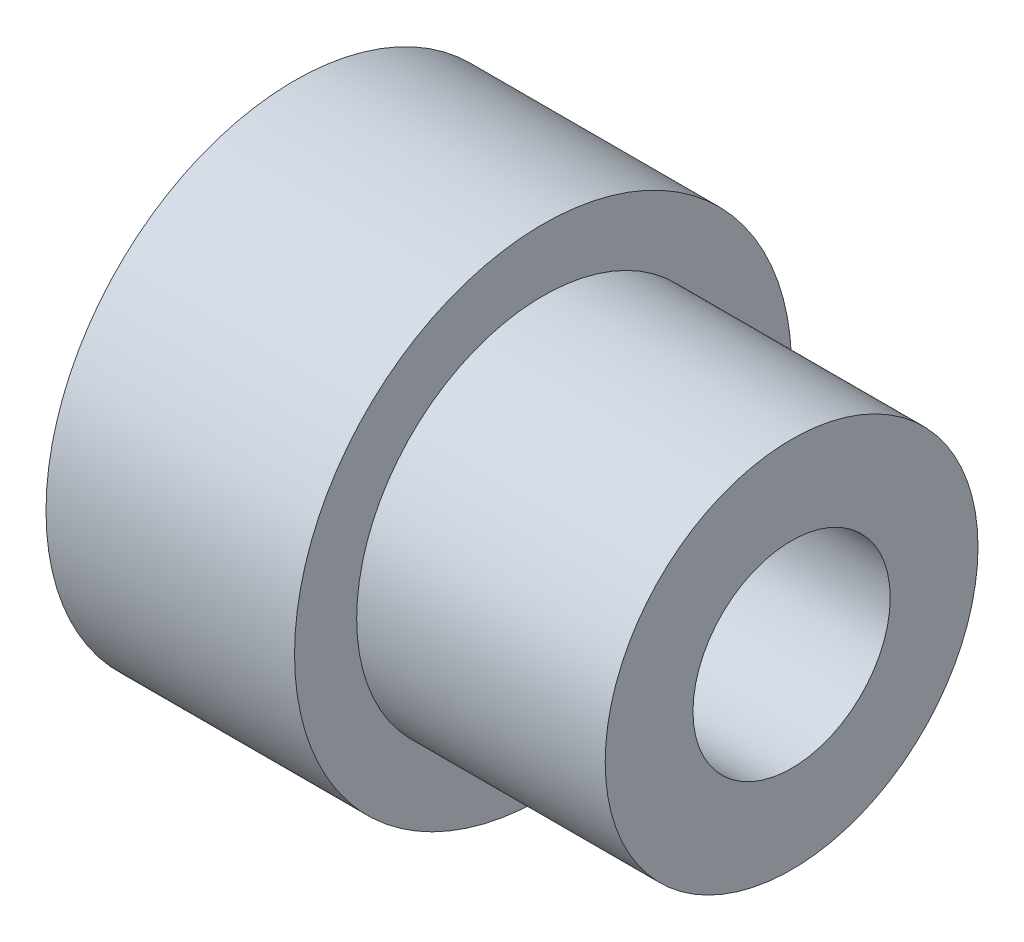
SolidWorks part; units mm, degrees
ref_plane "Front Plane" through (0, 0, 0) normal (0, 0, 1) x (1, 0, 0)
ref_plane "Top Plane" through (0, 0, 0) normal (0, 1, 0) x (1, 0, 0)
ref_plane "Right Plane" through (0, 0, 0) normal (1, 0, 0) x (0, 0, -1)
sketch "Sketch2" plane through (0, 0, 0) normal (1, 0, 0) x (0, 0, -1)
  circle A0 centre (0, 0) radius 6
  dimension "D1" = 12
extrude "Boss-Extrude1" add sketch "Sketch2" along normal blind 8
sketch "Sketch3" plane through (0, 0, 0) normal (-1, 0, 0) x (0, 0, 1)
  circle A0 centre (0, 0) radius 8
  dimension "D1" = 16
extrude "Boss-Extrude2" add sketch "Sketch3" along normal blind 8
sketch "Sketch4" plane through (8, 0, 0) normal (1, 0, 0) x (0, 0, -1)
  circle A0 centre (0, 0) radius 3.175
  dimension "D1" = 6.35
extrude "Cut-Extrude1" cut sketch "Sketch4" against normal through all
equation "\"wheelPitchD\"= 16mm"
equation "\"wheelClearanceD\"= 18mm"
equation "\"wormPitchD\"= 12mm"
equation "\"wormClearanceD\"= 14mm"
equation "\"D1@Sketch3\"=\"wheelPitchD\""
equation "\"D1@Sketch2\"=\"HubDiameter\""
equation "\"ShaftD\"= 0.25in"
equation "\"D1@Sketch4\"=\"ShaftD\""
equation "\"MountingDistance\" = 14mm"
equation "\"HubDiameter\"= 12mm"
equation "\"HubWidth\"= 8mm"
equation "\"FaceWidth\"= 8mm"
equation "\"D1@Boss-Extrude1\"=\"FaceWidth\""
equation "\"D1@Boss-Extrude2\"=\"HubWidth\""
